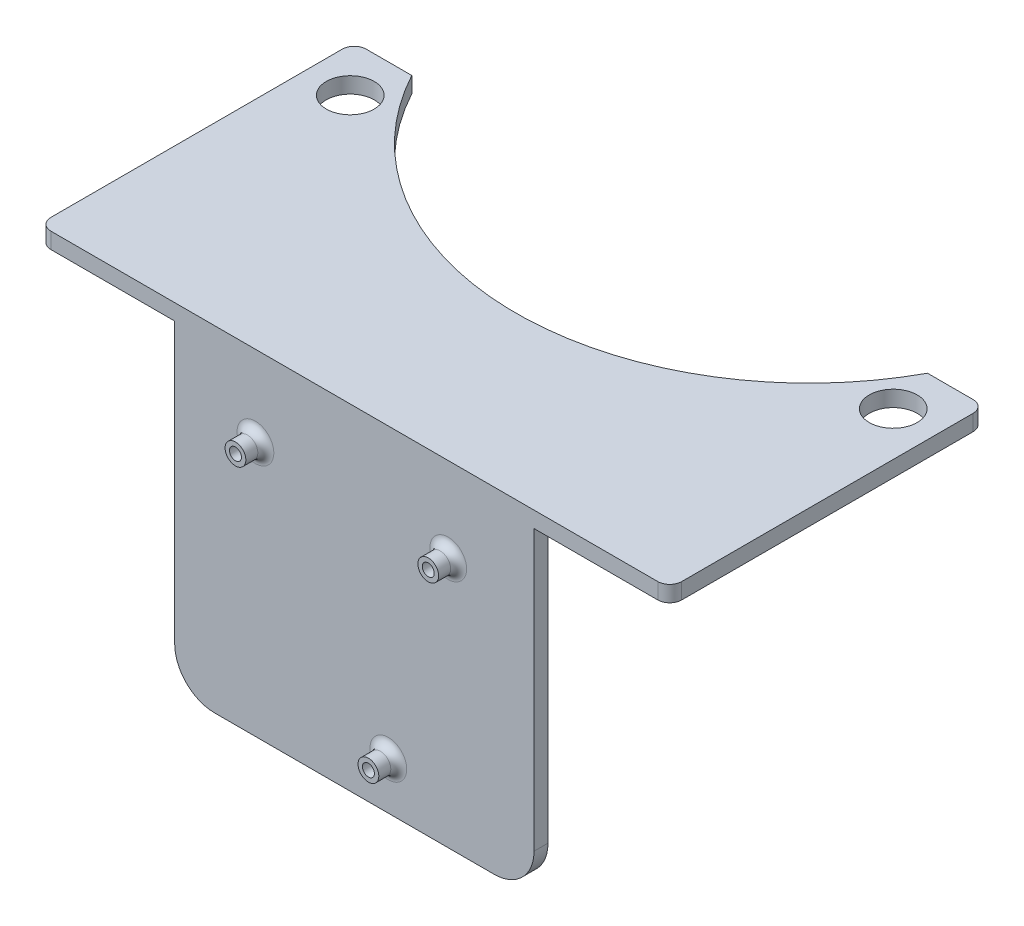
SolidWorks part; units mm, degrees
ref_plane "前视基准面" through (0, 0, 0) normal (0, 0, 1) x (1, 0, 0)
ref_plane "上视基准面" through (0, 0, 0) normal (0, 1, 0) x (1, 0, 0)
ref_plane "右视基准面" through (0, 0, 0) normal (1, 0, 0) x (0, 0, -1)
sketch "摄像头底座" plane through (0, 0, 0) normal (0, 1, 0) x (1, 0, 0)
  line L2 (79, 11.5207) -> (79, 84.4921)
  line L3 (76, 87.4921) -> (64.5887, 87.4921)
  line L4 (-79, 11.5207) -> (-79, 84.4921)
  line L6 (0, 3.3836) -> (0, 48.9763) construction
  line L9 (0, 0) -> (0, -22.765) construction
  line L10 (0, -22.765) -> (0, 0) construction
  line L11 (-76, 8.5207) -> (76.0029, 8.5207)
  line L12 (-64.5887, 87.4921) -> (-76, 87.4921)
  circle A2 centre (68, 75.4921) radius 6
  circle A3 centre (-68, 75.4921) radius 6
  arc A7 (-79, 84.4921) -> (-76, 87.4921) centre (-76, 84.4921) cw
  arc A8 (79, 84.4921) -> (76, 87.4921) centre (76, 84.4921) ccw
  arc A9 (79, 11.5207) -> (76.0029, 8.5207) centre (76, 11.5207) cw
  arc A10 (-79, 11.5207) -> (-76, 8.5207) centre (-76, 11.5207) ccw
  arc A11 (-64.5887, 87.4921) -> (64.5887, 87.4921) centre (0, 122.3899) ccw
  point P0 (0, 0)
  point P4 (0, 0)
  point P7 (0, 0)
  point P8 (0, -24.3708)
  point P9 (0, 0)
  point P10 (0, 0)
  point P11 (0, 48.9763)
  dimension "D2" = 136
  dimension "D5" = 3
  dimension "D6" = 3
  dimension "D1" = 158
  dimension "D3" = 12
extrude "凸台-拉伸1" add sketch "摄像头底座" along normal blind 4
sketch "草图2" plane through (0, 0, 0) normal (1, 0, 0) x (0, 0, -1)
  line L30 (8.5207, 0) -> (12.0207, 0)
  line L31 (11.5207, 0) -> (84.4921, 0) construction
  line L32 (12.0207, 0) -> (12.0207, -80)
  line L33 (12.0207, -80) -> (8.5207, -80)
  line L34 (8.5207, -80) -> (8.5207, 0)
  dimension "D1" = 3.5
  dimension "D2" = 80
extrude "凸台-拉伸3" add sketch "草图2" along normal mid plane 90
sketch "草图10" plane through (0, 0, -8.5207) normal (0, 0, 1) x (1, 0, 0)
  circle A6 centre (23.5119, -17.208) radius 2.6
  circle A7 centre (-24.7777, -16.208) radius 2.6
  circle A8 centre (8.5243, -68.1489) radius 2.6
  circle A9 centre (23.5119, -17.208) radius 1.5
  circle A10 centre (-24.7777, -16.208) radius 1.5
  circle A11 centre (8.5243, -68.1489) radius 1.5
sketch "草图11" plane through (0, 0, 0) normal (1, 0, 0) x (0, 0, -1)
  line L0 (11.5207, 0) -> (84.4921, 0) construction
  line L1 (22.5195, 0) -> (25.3195, 0)
  line L2 (22.5195, 0) -> (22.5195, -13.2964)
  line L4 (25.3195, 0) -> (25.3195, -13.2903)
  line L5 (22.5195, -13.2964) -> (12.0207, -25.1371)
  line L6 (12.0207, -80) -> (12.0207, 0) construction
  line L7 (12.0207, -25.1371) -> (12.0207, -28.2889)
  line L8 (12.0207, -28.2889) -> (25.3195, -13.2903)
  dimension "D1" = 2.8
extrude "凸台-拉伸4" add sketch "草图11" along normal mid plane 29
extrude "凸台-拉伸5" add sketch "草图10" along normal blind 5
fillet "圆角1" radius 2 1 edges at (5.9243, -68.1489, -8.5207)
fillet "圆角2" radius 2 2 edges at (-27.3777, -16.208, -8.5207) (20.9119, -17.208, -8.5207)
fillet "圆角3" radius 10 1 edges at (45, -80, -10.2707)
fillet "圆角4" radius 10 1 edges at (-45, -80, -10.2707)
fillet "圆角5" radius 5 1 edges at (0, 0, -25.3195)
sketch "草图12" plane through (0, 0, -8.5207) normal (0, 0, 1) x (1, 0, 0)
  circle A0 centre (-24.7777, -16.208) radius 1.5
  circle A1 centre (23.5119, -17.208) radius 1.5
  circle A2 centre (8.5243, -68.1489) radius 1.5
extrude "切除-拉伸1" cut sketch "草图12" against normal blind 5
